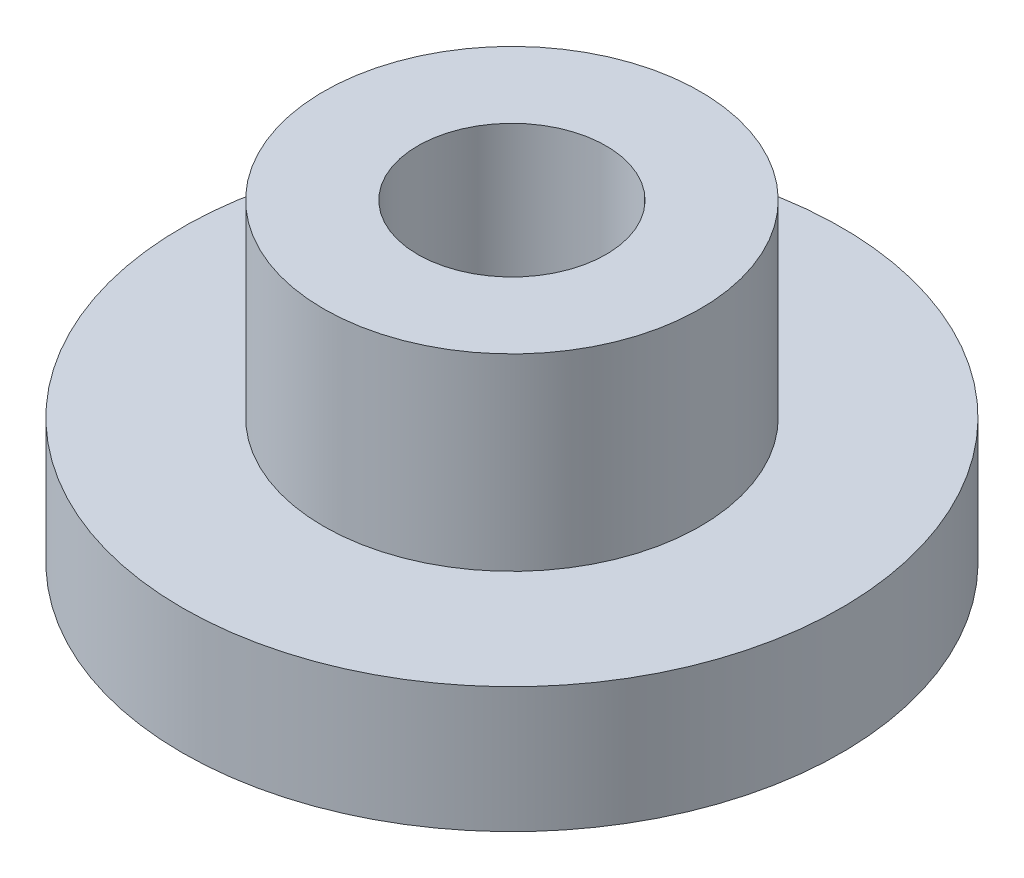
SolidWorks part; units mm, degrees
material "AISI 1020 Acier laminé à froid"
ref_plane "Plan de face" through (0, 0, 0) normal (0, 0, 1) x (1, 0, 0)
ref_plane "Plan de dessus" through (0, 0, 0) normal (0, 1, 0) x (1, 0, 0)
ref_plane "Plan de droite" through (0, 0, 0) normal (1, 0, 0) x (0, 0, -1)
sketch "Esquisse1" plane through (0, 0, 0) normal (0, 0, 1) x (1, 0, 0)
  line L0 (0, 27.2703) -> (0, -21.4895) construction
  line L1 (0, -2) -> (-5.25, -2)
  line L2 (-5.25, -2) -> (-5.25, 0)
  line L3 (-5.25, 0) -> (-3, 0)
  line L4 (-3, 0) -> (-3, 3)
  line L5 (-3, 3) -> (-1.5, 3)
  line L6 (-1.5, 3) -> (-1.5, 0.866)
  line L7 (-1.5, 0.866) -> (0, 0)
  line L8 (0, 0) -> (0, -2)
  dimension "D1" = 60
  dimension "D2" = 1.5
  dimension "D3" = 3
  dimension "D4" = 2
  dimension "D5" = 5.25
  dimension "D6" = 3
revolve "Révolution1" add sketch "Esquisse1" angle 360 about L0
